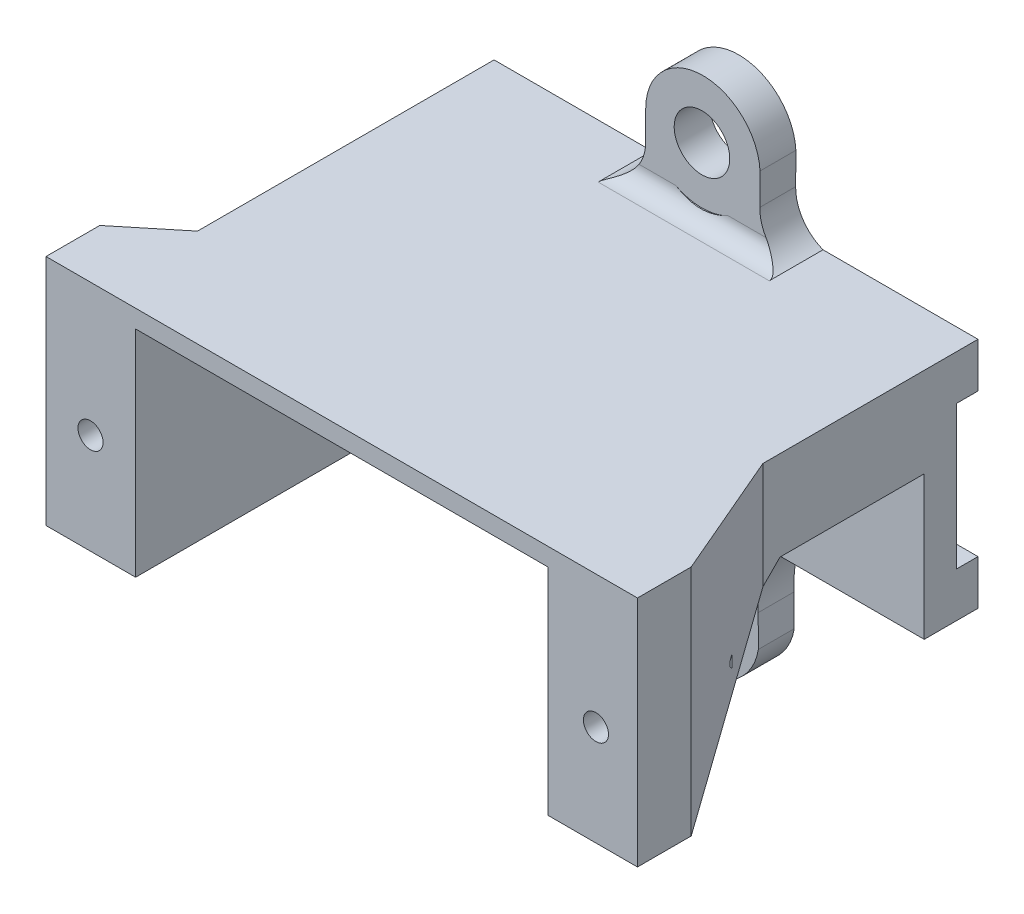
SolidWorks part; units mm, degrees
ref_plane "Front Plane" through (0, 0, 0) normal (0, 0, 1) x (1, 0, 0)
ref_plane "Top Plane" through (0, 0, 0) normal (0, 1, 0) x (1, 0, 0)
ref_plane "Right Plane" through (0, 0, 0) normal (1, 0, 0) x (0, 0, -1)
imported_body "Surface-Imported1" [suppressed]
sketch "Sketch1" plane through (0, 0, 0) normal (0, 1, 0) x (1, 0, 0)
  line L12 (-20.6282, -9.5718) -> (-20.6282, -11.5718)
  line L13 (-20.6282, -11.5718) -> (-15.7282, -11.5718)
  line L14 (12.3718, -11.5718) -> (12.3718, -9.5718)
  line L15 (12.3718, -9.5718) -> (9.3718, -2.5718)
  line L16 (9.3718, -2.5718) -> (9.3718, 6.4282)
  line L17 (9.3718, 6.4282) -> (-17.6282, 6.4282)
  line L18 (-17.6282, 6.4282) -> (-17.6282, -7.1192)
  line L19 (-17.6282, -7.1192) -> (-20.6282, -9.5718)
  line L21 (-15.6282, 4.4282) -> (7.3718, 4.4282)
  line L23 (7.4718, -11.5718) -> (12.3718, -11.5718)
  line L24 (-15.7282, -11.5718) -> (-15.6282, -11.5718)
  line L25 (-15.6282, -11.5718) -> (-15.6282, 4.4282)
  line L26 (7.4718, -11.5718) -> (7.3718, -11.5718)
  line L27 (7.3718, -11.5718) -> (7.3718, 4.4282)
  line L28 (9.3718, 6.4282) -> (9.3718, 9.4282) construction
  line L30 (-17.6282, 6.4282) -> (9.3718, 6.4282)
  line L31 (-17.6282, 6.4282) -> (-17.6282, 9.4282)
  line L32 (-17.6282, 9.4282) -> (9.3718, 9.4282)
  line L33 (9.3718, 6.4282) -> (9.3718, 9.4282)
  dimension "D1" = 3
extrude "Boss-Extrude1" add sketch "Sketch1" along normal blind 12 contours L17 L33 L32 L31 | L27 L26 L23 L14 L15 L16 L17 L18 L19 L12 L13 L24 L25 L21
sketch "Sketch4" plane through (12.3718, 0, 0) normal (1, 0, 0) x (0, 0, -1)
  line L0 (4.4282, 0) -> (4.4282, 8)
  line L2 (-2.5718, 8) -> (-9.5718, 0) construction
  line L3 (-9.5718, 0) -> (-11.5718, 0)
  line L4 (-11.5718, 0) -> (4.4282, 0)
  line L7 (-2.5718, 8) -> (-1.6187, 8) construction
  line L8 (-9.5718, 0) -> (-1.6187, 8)
  line L11 (-1.6187, 8) -> (4.4282, 8)
extrude "Cut-Extrude1" cut sketch "Sketch4" against normal blind 11.5
sketch "Sketch5" plane through (0, 12, 0) normal (0, 1, 0) x (1, 0, 0)
  line L0 (-20.6282, -11.5718) -> (-20.6282, -9.5718)
  line L2 (-20.6282, -9.5718) -> (-17.6282, -7.1192)
  line L3 (-17.6282, -7.1192) -> (-17.6282, 6.4282)
  line L4 (-17.6282, 6.4282) -> (9.3718, 6.4282)
  line L5 (9.3718, 6.4282) -> (9.3718, -2.5718)
  line L6 (9.3718, -2.5718) -> (12.3718, -9.5718)
  line L7 (12.3718, -9.5718) -> (12.3718, -11.5718)
  line L8 (12.3718, -11.5718) -> (-20.6282, -11.5718)
  line L10 (-17.6282, 6.4282) -> (9.3718, 6.4282)
  line L11 (-17.6282, 6.4282) -> (-17.6282, 9.4282)
  line L12 (-17.6282, 9.4282) -> (9.3718, 9.4282)
  line L13 (9.3718, 6.4282) -> (9.3718, 9.4282)
  line M27 (-17.6282, 9.4282) -> (-17.6282, -7.1192)
  line M28 (-17.6282, -7.1192) -> (-20.6282, -9.5718)
  line M29 (-20.6282, -9.5718) -> (-20.6282, -11.5718)
  line M30 (-20.6282, -11.5718) -> (-15.6282, -11.5718)
  line M31 (-15.6282, -11.5718) -> (-15.6282, 4.4282)
  line M32 (-15.6282, 4.4282) -> (7.3718, 4.4282)
  line M33 (7.3718, 4.4282) -> (7.3718, -11.5718)
  line M34 (7.3718, -11.5718) -> (12.3718, -11.5718)
  line M35 (12.3718, -11.5718) -> (12.3718, -9.5718)
  line M36 (12.3718, -9.5718) -> (9.3718, -2.5718)
  line M37 (9.3718, -2.5718) -> (9.3718, 9.4282)
  line M38 (9.3718, 9.4282) -> (-17.6282, 9.4282)
extrude "Boss-Extrude2" add sketch "Sketch5" along normal blind 1 contours L4 M27 M28 M29 M30 M31 M32 M33 M34 M35 M36 M37 | L4 M27 M37 M38
sketch "Sketch7" plane through (0, 0, 11.5718) normal (0, 0, 1) x (1, 0, 0)
  line L0 (-15.6446, 0.1026) -> (12.4554, 0.1026) construction
  line L3 (-20.5446, 11.6026) -> (12.4554, 11.6026) construction
  line L4 (-20.5446, 11.6026) -> (-20.5446, 0.1026) construction
  line L5 (-20.5446, 0.1026) -> (12.4554, 0.1026) construction
  line L6 (12.4554, 11.6026) -> (12.4554, 0.1026) construction
  circle A0 centre (-18.1446, 5.6026) radius 0.7
  circle A1 centre (10.0554, 5.6026) radius 0.7
  dimension "D1" = 1.4
  dimension "D2" = 1.4
extrude "Cut-Extrude2" cut sketch "Sketch7" against normal blind 6
move or copy body "Body-Move/Copy1" [suppressed] bodies to move or copy 101 copy no translate (-980.2029, 45.892, 0)
sketch "Sketch8" plane through (0, 0, -9.4282) normal (0, 0, -1) x (-1, 0, 0)
  line L0 (0.7894, 17.0512) -> (0.8013, 15.2867)
  line L1 (7.1674, 15.2812) -> (7.1674, 16.8812)
  line L4 (-7.6494, 5.6029) -> (15.6486, 5.6029) construction
  line L5 (4.0304, 16.7989) -> (4.0304, -5.5931) construction
  line L8 (7.1706, -4.5615) -> (7.1706, -6.1615)
  line L9 (0.8812, -6.1098) -> (0.8932, -4.3398)
  line L11 (-10.0554, 5.6026) -> (18.1446, 5.6026) construction
  line L12 (8.8216, 13) -> (8.8216, 0.3529) construction
  line L13 (-0.7244, 13) -> (-0.7244, 0.2714) construction
  line L15 (0.8013, 15.2867) -> (7.1674, 15.2812) construction
  line L16 (-0.7244, 0.2714) -> (-0.7244, 0) construction
  line L17 (-9.3718, 13) -> (17.6282, 13) construction
  line L19 (8.8216, 0.3529) -> (8.8216, 0) construction
  line L20 (-49.169, 17.6196) -> (-49.157, 15.8496)
  line L21 (-42.791, 15.8496) -> (-42.791, 17.4496)
  line L22 (-50.737, 14.2496) -> (-41.191, 14.2576)
  line L23 (-57.662, 6.2536) -> (-34.364, 6.2536) construction
  line L24 (-50.737, -1.7424) -> (-41.191, -1.7504)
  line L25 (-42.791, -3.3424) -> (-42.791, -4.9424)
  line L26 (-49.169, -5.1124) -> (-49.157, -3.3424)
  line L27 (-45.9823, 17.4496) -> (-45.9823, -4.9424) construction
  circle A0 centre (4.0304, 16.7935) radius 1.5498
  arc A4 (0.7894, 17.0512) -> (7.1674, 16.8812) centre (3.9761, 16.8812) cw
  arc A5 (0.8812, -6.1098) -> (7.1706, -6.1615) centre (4.0304, -5.5931) ccw
  circle A8 centre (4.0304, -5.5931) radius 1.5498
  arc A10 (-0.7244, 0) -> (0.8932, -4.3398) centre (-4.6932, -3.9507) cw
  arc A11 (7.1706, -4.5615) -> (8.8216, 0) centre (12.7422, -3.9986) cw
  arc A12 (0.8013, 15.2867) -> (-0.7244, 13) centre (-1.5981, 15.2353) cw
  arc A13 (7.1674, 15.2812) -> (8.8216, 13) centre (9.5674, 15.2812) ccw
  circle A14 centre (-45.9745, 17.4489) radius 1.5498
  arc A15 (-49.157, 15.8496) -> (-50.737, 14.2496) centre (-50.9165, 16.007) cw
  arc A16 (-42.791, 15.8496) -> (-41.191, 14.2576) centre (-40.9874, 16.0623) ccw
  arc A17 (-49.169, 17.6196) -> (-42.791, 17.4496) centre (-45.9823, 17.4496) cw
  arc A18 (-49.169, -5.1124) -> (-42.791, -4.9424) centre (-45.9823, -4.9424) ccw
  arc A19 (-42.791, -3.3424) -> (-41.191, -1.7504) centre (-40.9874, -3.555) cw
  arc A20 (-49.157, -3.3424) -> (-50.737, -1.7424) centre (-50.9165, -3.4997) ccw
  circle A21 centre (-45.9745, -4.9416) radius 1.5498
  point P21 (4.0304, 16.7989)
  point P40 (3.9996, 5.6029)
  point P63 (-45.964, 14.2536)
  point P64 (-45.964, 14.2536)
  point P74 (-45.964, -1.7464)
extrude "Boss-Extrude3" add sketch "Sketch8" against normal blind 2
sketch "Sketch11" plane through (0, 0, -9.4282) normal (0, 0, -1) x (-1, 0, 0)
  line L0 (4.0304, -5.5931) -> (4.0304, 16.7935) construction
  line L1 (20.6282, 6.5) -> (-12.3718, 6.5) construction
  line L2 (20.6282, 13) -> (20.6282, 0) construction
  line L3 (-12.3718, 13) -> (-12.3718, 0) construction
  line L5 (19.5101, 10.5) -> (-11.2537, 10.5)
  line L6 (19.5101, 10.5) -> (19.5101, 2.5)
  line L7 (19.5101, 2.5) -> (-11.2537, 2.5)
  line L8 (-11.2537, 10.5) -> (-11.2537, 2.5)
  line L9 (19.5101, 10.5) -> (-11.2537, 2.5) construction
  line L10 (19.5101, 2.5) -> (-11.2537, 10.5) construction
  point P10 (4.1282, 6.5)
  dimension "D1" = 8
extrude "Cut-Extrude3" cut sketch "Sketch11" against normal blind 1.2
fillet "Fillet1" radius 1 2 edges at (-4.0486, 13, -7.4282) (-4.0486, 0, -7.4282)
sketch "Sketch12" plane through (0, 0, -7.4282) normal (0, 0, 1) x (1, 0, 0)
  circle A0 centre (-4.0304, 16.7935) radius 3.1536
extrude "Cut-Extrude4" cut sketch "Sketch12" along normal blind 10
sketch "Sketch13" plane through (0, 0, -4.4282) normal (0, 0, 1) x (1, 0, 0)
  line L0 (-15.6282, 0) -> (-15.6282, 12)
  line L1 (-15.6282, 12) -> (7.3718, 12)
  line L2 (7.3718, 12) -> (7.3718, 0) construction
  line L3 (7.3718, 12) -> (7.3718, 8) construction
  line L4 (7.3718, 12) -> (7.3718, 8)
  line L5 (7.3718, 0) -> (-15.6282, 0)
  line L6 (7.3718, 8) -> (9.3718, 8)
  line L7 (9.3718, 8) -> (9.3718, 0)
  line L8 (9.3718, 0) -> (7.3718, 0)
extrude "Cut-Extrude5" cut sketch "Sketch13" against normal blind 2
sketch "Sketch14" plane through (0, 0, 11.5718) normal (0, 0, 1) x (1, 0, 0)
  line L0 (-20.6282, 0) -> (-20.6282, 13)
  line L1 (-20.6282, 13) -> (12.3718, 13)
  line L2 (12.3718, 13) -> (12.3718, 0)
  line L3 (12.3718, 0) -> (7.3718, 0)
  line L4 (7.3718, 0) -> (7.3718, 12)
  line L5 (7.3718, 8) -> (7.3718, 12) construction
  line L6 (7.3718, 12) -> (7.3718, 0) construction
  line L7 (7.3718, 12) -> (-15.6282, 12)
  line L8 (-15.6282, 12) -> (-15.6282, 0)
  line L9 (-15.6282, 0) -> (-20.6282, 0)
  circle A0 centre (-18.1446, 5.6026) radius 0.7
  circle A1 centre (10.0554, 5.6026) radius 0.7
extrude "Boss-Extrude4" add sketch "Sketch14" along normal blind 1
equation "\"standoff\"=3"
equation "\"D1@Sketch1\"=\"standoff\""
